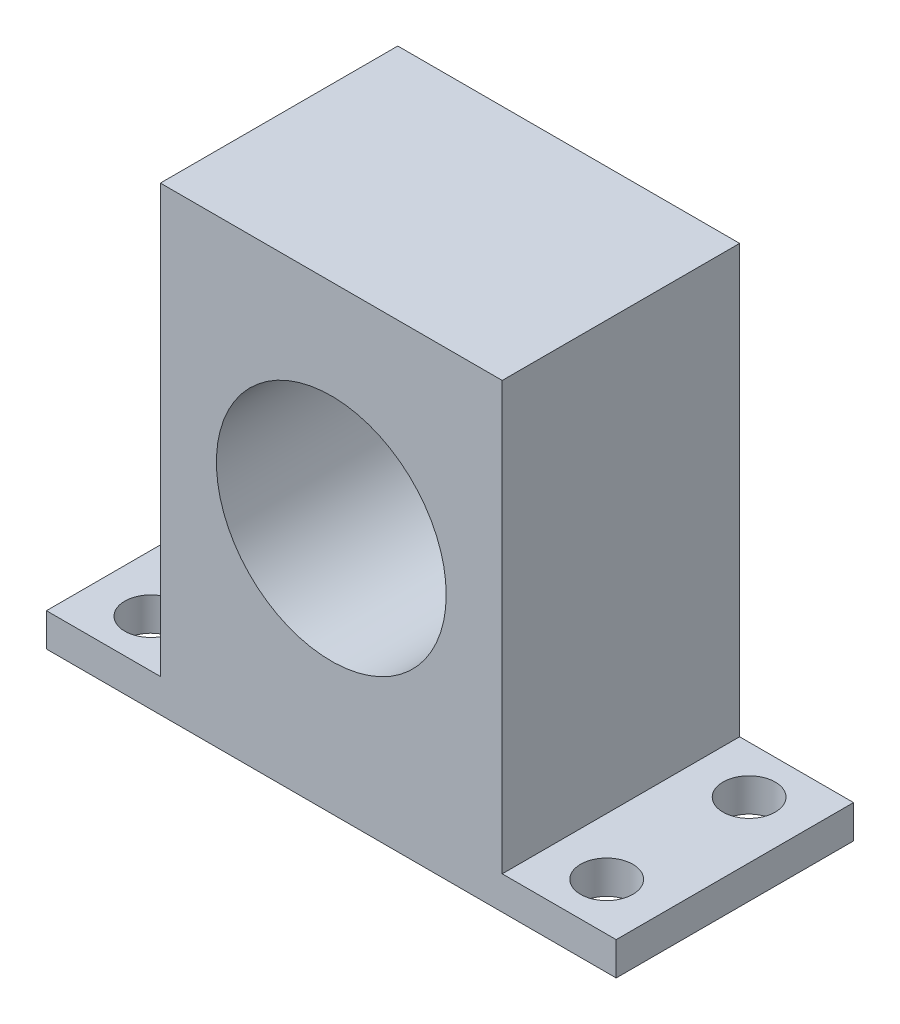
SolidWorks part; units mm, degrees
ref_plane "Front" through (0, 0, 0) normal (0, 0, 1) x (1, 0, 0)
ref_plane "Top" through (0, 0, 0) normal (0, 1, 0) x (1, 0, 0)
ref_plane "Right" through (0, 0, 0) normal (1, 0, 0) x (0, 0, -1)
sketch "Sketch3" plane through (0, 0, 0) normal (0, 0, 1) x (1, 0, 0)
  line L1 (0, 0) -> (18, 0)
  line L2 (0, 0) -> (0, 22.5)
  line L3 (0, 22.5) -> (18, 22.5)
  line L4 (18, 0) -> (18, 22.5)
  dimension "D1" = 18
  dimension "D2" = 22.5
extrude "bracketBase" add sketch "Sketch3" along normal blind 12.5
sketch "Sketch4" plane through (0, 0, 12.5) normal (0, 0, 1) x (1, 0, 0)
  line L0 (0, 0) -> (18, 0) construction
  line L1 (9, 0) -> (9, 22.5) construction
  line L2 (18, 22.5) -> (0, 22.5) construction
  circle A0 centre (9, 11.25) radius 6.05
  dimension "D1" = 12.1
  dimension "D2" = 11.25
extrude "hole" cut sketch "Sketch4" against normal through all
sketch "Sketch5" plane through (0, 0, 0) normal (0, -1, 0) x (1, 0, 0)
  line L0 (0, 12.5) -> (18, 12.5) construction
  line L1 (-6, 0) -> (24, 0)
  line L2 (-6, 0) -> (-6, 12.5)
  line L3 (-6, 12.5) -> (24, 12.5)
  line L4 (24, 0) -> (24, 12.5)
  line L5 (0, 0) -> (18, 0) construction
  line L7 (18, 12.5) -> (18, 0) construction
  line L8 (0, 12.5) -> (0, 0) construction
  dimension "D1" = 6
  dimension "D2" = 6
extrude "tabBase" add sketch "Sketch5" along normal blind 1.75
sketch "Sketch6" plane through (0, 0, 0) normal (0, 1, 0) x (1, 0, 0)
  line L0 (-3, 0) -> (-3, -12.5) construction
  line L1 (-6, 0) -> (0, 0) construction
  line L2 (0, -12.5) -> (-6, -12.5) construction
  line L3 (21, 0) -> (21, -12.5) construction
  line L4 (18, 0) -> (24, 0) construction
  line L5 (24, -12.5) -> (18, -12.5) construction
  line L6 (9, 0) -> (9, -12.5) construction
  line L7 (18, 0) -> (0, 0) construction
  line L8 (18, -12.5) -> (0, -12.5) construction
  circle A0 centre (-3, -2.5) radius 1.375
  circle A1 centre (-3, -10) radius 1.375
  circle A2 centre (21, -2.5) radius 1.375
  circle A3 centre (21, -10) radius 1.375
  dimension "D1" = 2.75
  dimension "D2" = 2.5
  dimension "D3" = 2.5
extrude "mountingHoles" cut sketch "Sketch6" against normal through all
